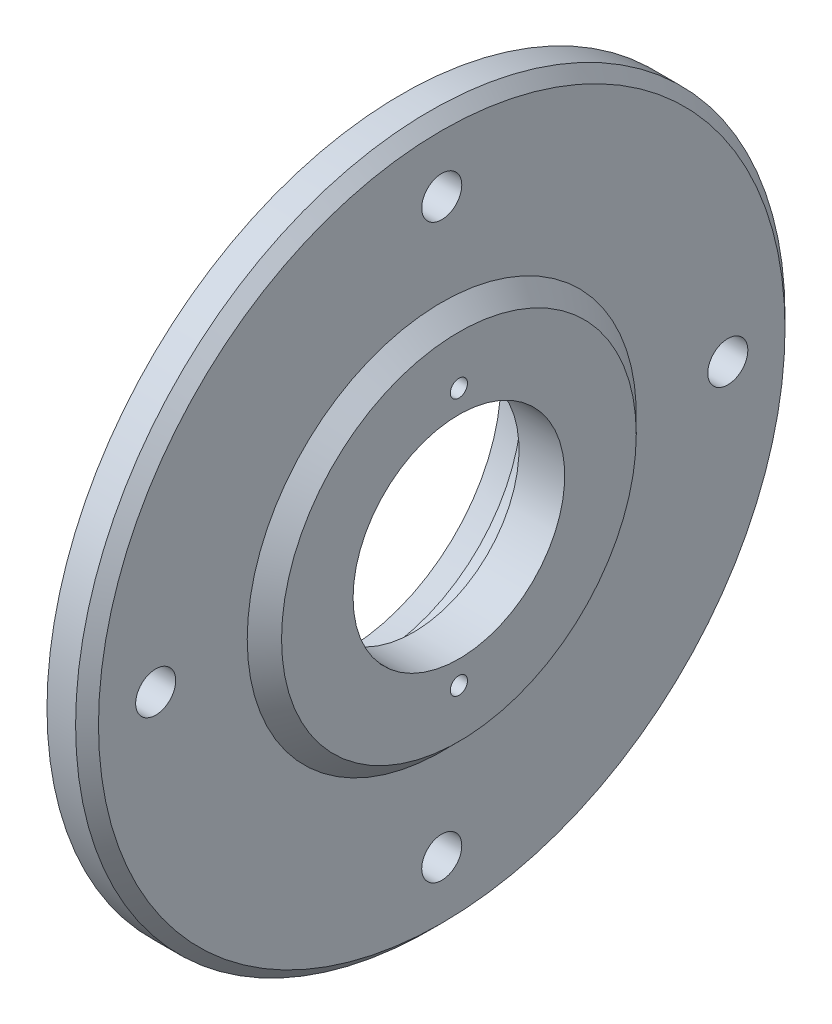
SolidWorks part; units mm, degrees
ref_plane "Přední rovina" through (0, 0, 0) normal (0, 0, 1) x (1, 0, 0)
ref_plane "Vrchní rovina" through (0, 0, 0) normal (0, 1, 0) x (1, 0, 0)
ref_plane "Pravá rovina" through (0, 0, 0) normal (1, 0, 0) x (0, 0, -1)
sketch "Skica1" plane through (0, 0, 0) normal (0, 0, 1) x (1, 0, 0)
  line L0 (-2, 62) -> (-2, 34)
  line L1 (-2, 62) -> (5, 62)
  line L2 (5, 62) -> (5, 34)
  line L3 (5, 34) -> (8, 31)
  line L4 (8, 31) -> (8, 18.5)
  line L5 (-2, 34) -> (-12, 34)
  line L6 (-12, 34) -> (-12, 27.3397)
  line L7 (0, 26) -> (-7, 26)
  line L8 (0, 26) -> (0, 18.5)
  line L9 (-20.7775, 0) -> (48.5362, 0) construction
  line L10 (8, 18.5) -> (0, 18.5)
  line L11 (-7, 26) -> (-12, 27.3397)
  point P1 (0, 0)
  point P2 (0, 0)
  point P15 (0, 0)
  point P16 (0, 0)
  point P17 (0, 0)
  dimension "D1" = 62
  dimension "D2" = 20
  dimension "D3" = 124
  dimension "D4" = 68
  dimension "D5" = 52
  dimension "D6" = 12
  dimension "D7" = 3
  dimension "D8" = 45
  dimension "D9" = 15
  dimension "D10" = 5
  dimension "D11" = 10
  dimension "D12" = 37
revolve "Rotovat1" add sketch "Skica1" angle 360 about L9
chamfer "Zkosení1" distance 2 angle 45 1 edges at (5, 0, 62)
sketch "Skica2" plane through (8, 0, 0) normal (1, 0, 0) x (0, 0, -1)
  circle A0 centre (0, 0) radius 22.5 construction
  circle A1 centre (0, 22.5) radius 1.5
  dimension "D1" = 3
  dimension "D2" = 45
extrude "Odebrat vysunutím1" cut sketch "Skica2" against normal up to next (8 mm away)
pattern_circular "Kruhové pole1" count 2 over 360 about axis through (0, 0, 0) along (1, 0, 0) of "Odebrat vysunutím1"
sketch "Skica3" plane through (5, 0, 0) normal (1, 0, 0) x (0, 0, -1)
  circle A0 centre (0, 0) radius 50 construction
  circle A1 centre (0, 50) radius 3.5
  dimension "D1" = 100
  dimension "D2" = 7
extrude "Odebrat vysunutím2" cut sketch "Skica3" against normal up to next (7 mm away)
pattern_circular "Kruhové pole2" count 4 over 360 about axis through (0, 0, 0) along (1, 0, 0) of "Odebrat vysunutím2"
